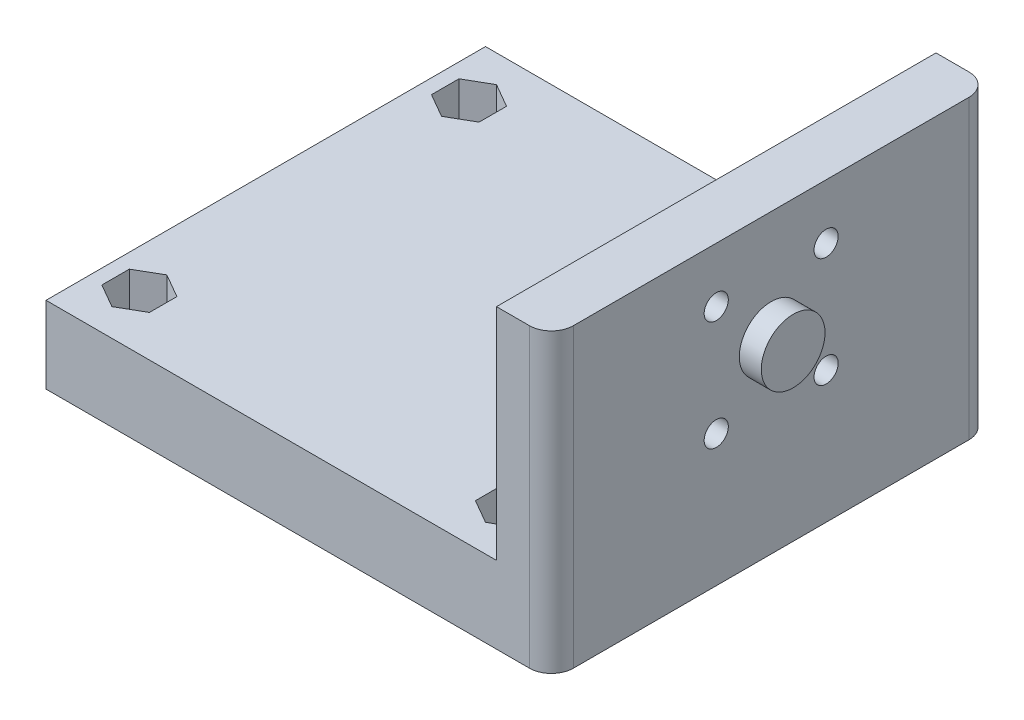
SolidWorks part; units mm, degrees
ref_plane "Plan de face" through (0, 0, 0) normal (0, 0, 1) x (1, 0, 0)
ref_plane "Plan de dessus" through (0, 0, 0) normal (0, 1, 0) x (1, 0, 0)
ref_plane "Plan de droite" through (0, 0, 0) normal (1, 0, 0) x (0, 0, -1)
sketch "Esquisse1" plane through (0, 0, 0) normal (0, 1, 0) x (1, 0, 0)
  line L1 (0, 20) -> (-5, 20)
  line L2 (0, 20) -> (0, -20)
  line L3 (0, -20) -> (-5, -20)
  line L4 (-5, 20) -> (-5, -20)
  dimension "D1" = 5
  dimension "D2" = 40
  dimension "D3" = 20
extrude "Boss.-Extru.1" add sketch "Esquisse1" against normal blind 27
sketch "Esquisse2" plane through (-5, 0, 0) normal (-1, 0, 0) x (0, 0, 1)
  line L0 (-20, -27) -> (-20, 0) construction
  line L1 (20, -27) -> (-20, -27)
  line L2 (20, -27) -> (20, -20)
  line L3 (20, -20) -> (-20, -20)
  line L4 (-20, -27) -> (-20, -20)
  dimension "D1" = 7
extrude "Boss.-Extru.2" add sketch "Esquisse2" along normal blind 41
fillet "Congé1" radius 2 2 edges at (0, -13.5, -20) (0, -13.5, 20)
sketch "Esquisse4" plane through (0, 0, 0) normal (1, 0, 0) x (0, 0, -1)
  circle A0 centre (-5, -5) radius 1.1
  circle A1 centre (5, -5) radius 1.1
  circle A2 centre (-5, -15) radius 1.1
  circle A3 centre (5, -15) radius 1.1
  dimension "D1" = 10
  dimension "D3" = 2.2
  dimension "D2" = 10
  dimension "D4" = 5
  dimension "D5" = 5
extrude "Enlèv. mat.-Extru.1" cut sketch "Esquisse4" against normal up to next
sketch "Esquisse5" plane through (0, 0, 0) normal (1, 0, 0) x (0, 0, -1)
  line L1 (-18, 0) -> (18, 0) construction
  line L4 (20, 0) -> (20, -27) construction
  circle A0 centre (0, -10) radius 2.9
  dimension "D1" = 5.8
  dimension "D2" = 10
  dimension "D4" = 20
extrude "Boss.-Extru.3" add sketch "Esquisse5" along normal blind 2
sketch "Esquisse7" plane through (-5, 0, 0) normal (-1, 0, 0) x (0, 0, 1)
  line L1 (-3.75, -7.1651) -> (-2.5, -5)
  line L2 (-2.5, -5) -> (-3.75, -2.8349)
  line L3 (-3.75, -2.8349) -> (-6.25, -2.8349)
  line L4 (-6.25, -2.8349) -> (-7.5, -5)
  line L5 (-7.5, -5) -> (-6.25, -7.1651)
  line L6 (-6.25, -7.1651) -> (-3.75, -7.1651)
  line L7 (3.75, -2.8349) -> (2.5, -5)
  line L8 (2.5, -5) -> (3.75, -7.1651)
  line L9 (3.75, -7.1651) -> (6.25, -7.1651)
  line L10 (6.25, -7.1651) -> (7.5, -5)
  line L11 (7.5, -5) -> (6.25, -2.8349)
  line L12 (6.25, -2.8349) -> (3.75, -2.8349)
  line L13 (-3.75, -17.1651) -> (-2.5, -15)
  line L14 (-2.5, -15) -> (-3.75, -12.8349)
  line L15 (-3.75, -12.8349) -> (-6.25, -12.8349)
  line L16 (-6.25, -12.8349) -> (-7.5, -15)
  line L17 (-7.5, -15) -> (-6.25, -17.1651)
  line L18 (-6.25, -17.1651) -> (-3.75, -17.1651)
  line L19 (7.5, -15) -> (6.25, -12.8349)
  line L20 (6.25, -12.8349) -> (3.75, -12.8349)
  line L21 (3.75, -12.8349) -> (2.5, -15)
  line L22 (2.5, -15) -> (3.75, -17.1651)
  line L23 (3.75, -17.1651) -> (6.25, -17.1651)
  line L24 (6.25, -17.1651) -> (7.5, -15)
  line L25 (18, 0) -> (-18, 0) construction
  line L26 (-20, 0) -> (20, 0) construction
  circle A0 centre (-5, -5) radius 2.1651 construction
  circle A1 centre (5, -5) radius 2.1651 construction
  circle A2 centre (-5, -15) radius 2.1651 construction
  circle A3 centre (5, -15) radius 2.1651 construction
  circle A4 centre (5, -15) radius 1.1 construction
  dimension "D1" = 2.5
  dimension "D2" = 2.5
  dimension "D3" = 2.5
  dimension "D4" = 2.5
extrude "Enlèv. mat.-Extru.3" cut sketch "Esquisse7" against normal blind 3
sketch "Esquisse9" plane through (0, -20, 0) normal (0, 1, 0) x (1, 0, 0)
  line L0 (-5, -20) -> (-5, 20) construction
  line L1 (-46, -20) -> (-46, 20) construction
  line L4 (-46, -20) -> (-46, 20) construction
  circle A0 centre (-8.5, 15) radius 1.1
  circle A1 centre (-8.5, -15) radius 1.1
  circle A2 centre (-42.5, -15) radius 1.1
  circle A3 centre (-42.5, 15) radius 1.1
  point P8 (-46, 0)
  dimension "D1" = 2.2
  dimension "D5" = 15
  dimension "D2" = 3.5
  dimension "D3" = 3.5
  dimension "D4" = 30
extrude "Enlèv. mat.-Extru.5" cut sketch "Esquisse9" against normal through all
sketch "Esquisse8" plane through (0, -20, 0) normal (0, 1, 0) x (1, 0, 0)
  line L0 (-5, -20) -> (-5, 20) construction
  line L1 (-10.6651, 13.75) -> (-8.5, 12.5)
  line L2 (-8.5, 12.5) -> (-6.3349, 13.75)
  line L3 (-6.3349, 13.75) -> (-6.3349, 16.25)
  line L4 (-6.3349, 16.25) -> (-8.5, 17.5)
  line L5 (-8.5, 17.5) -> (-10.6651, 16.25)
  line L6 (-10.6651, 16.25) -> (-10.6651, 13.75)
  line L7 (-10.6651, -16.25) -> (-8.5, -17.5)
  line L8 (-8.5, -17.5) -> (-6.3349, -16.25)
  line L9 (-6.3349, -16.25) -> (-6.3349, -13.75)
  line L10 (-6.3349, -13.75) -> (-8.5, -12.5)
  line L11 (-8.5, -12.5) -> (-10.6651, -13.75)
  line L12 (-10.6651, -13.75) -> (-10.6651, -16.25)
  line L13 (-44.6651, -16.25) -> (-42.5, -17.5)
  line L14 (-42.5, -17.5) -> (-40.3349, -16.25)
  line L15 (-40.3349, -16.25) -> (-40.3349, -13.75)
  line L16 (-40.3349, -13.75) -> (-42.5, -12.5)
  line L17 (-42.5, -12.5) -> (-44.6651, -13.75)
  line L18 (-44.6651, -13.75) -> (-44.6651, -16.25)
  line L19 (-42.5, 12.5) -> (-40.3349, 13.75)
  line L20 (-40.3349, 13.75) -> (-40.3349, 16.25)
  line L21 (-40.3349, 16.25) -> (-42.5, 17.5)
  line L22 (-42.5, 17.5) -> (-44.6651, 16.25)
  line L23 (-44.6651, 16.25) -> (-44.6651, 13.75)
  line L24 (-44.6651, 13.75) -> (-42.5, 12.5)
  circle A0 centre (-8.5, 15) radius 2.1651 construction
  circle A1 centre (-8.5, -15) radius 2.1651 construction
  circle A2 centre (-42.5, -15) radius 2.1651 construction
  circle A3 centre (-42.5, 15) radius 2.1651 construction
  circle A4 centre (-8.5, 15) radius 1.1 construction
  circle A5 centre (-8.5, -15) radius 1.1 construction
  circle A7 centre (-42.5, 15) radius 1.1 construction
  dimension "D1" = 2.5
  dimension "D2" = 2.5
  dimension "D3" = 2.5
  dimension "D4" = 2.5
extrude "Enlèv. mat.-Extru.4" cut sketch "Esquisse8" against normal blind 4
